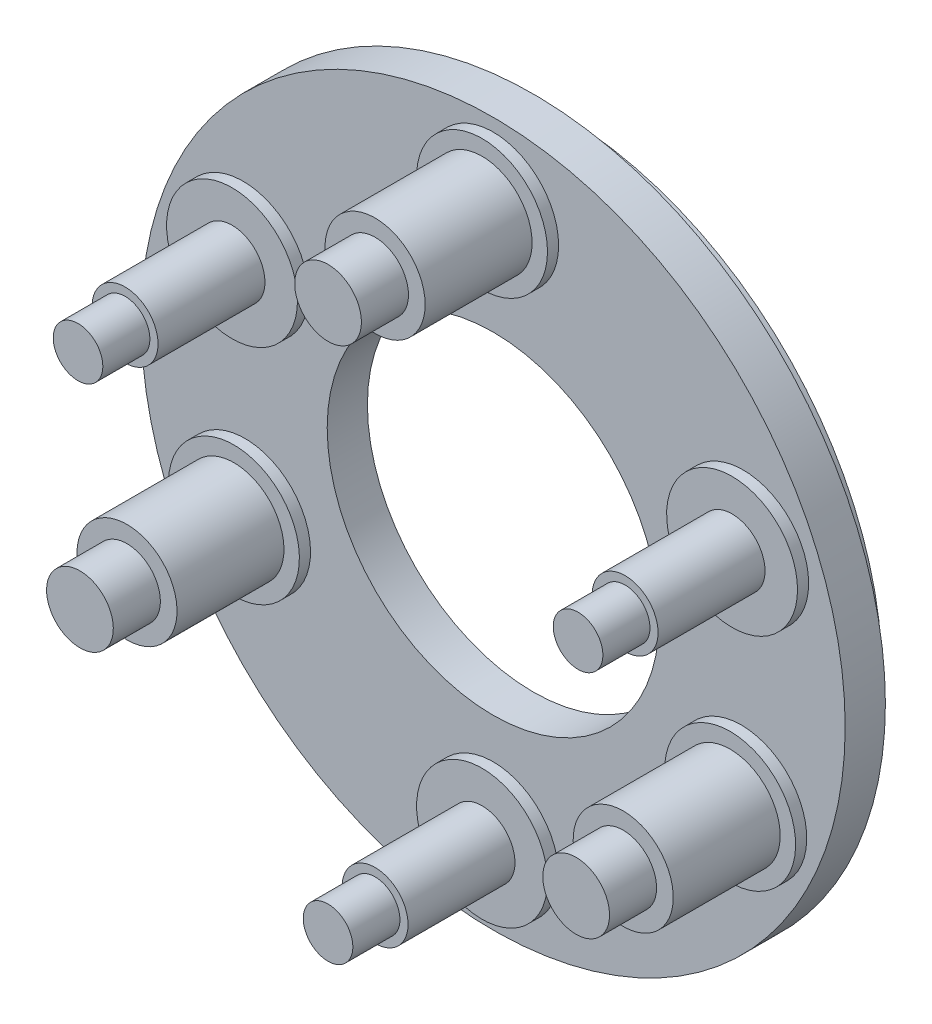
SolidWorks part; units mm, degrees
material "PE Low/Medium Density"
ref_plane "Front Plane" through (0, 0, 0) normal (0, 0, 1) x (1, 0, 0)
ref_plane "Top Plane" through (0, 0, 0) normal (0, 1, 0) x (1, 0, 0)
ref_plane "Right Plane" through (0, 0, 0) normal (1, 0, 0) x (0, 0, -1)
sketch "Sketch1" plane through (0, 0, 0) normal (0, 0, 1) x (1, 0, 0)
  circle A0 centre (0, 0) radius 10.4521
  circle A1 centre (0, 0) radius 4.9276
  dimension "D1" = 20.9042
  dimension "D2" = 9.8552
extrude "Base" add sketch "Sketch1" along normal blind 1.1938
sketch "Sketch2" plane through (0, 0, 0) normal (0, 0, -1) x (-1, 0, 0)
  circle A0 centre (0, 0) radius 9.6393
  circle A1 centre (0, 0) radius 8.89
  dimension "D1" = 17.78
  dimension "D2" = 0.7493
extrude "Track" add sketch "Sketch2" along normal blind 0.7112
sketch "Sketch3" plane through (0, 0, 1.1938) normal (0, 0, 1) x (1, 0, 0)
  line L0 (0, 0) -> (0, 10.4521) construction
  line L1 (0, 10.4521) -> (0, 0) construction
  circle A0 centre (0, 0) radius 10.4521 construction
  circle A1 centre (0, 8.128) radius 1.9431
  dimension "D1" = 3.8862
  dimension "D2" = 8.128
extrude "Platform A1" add sketch "Sketch3" along normal blind 0.3302
sketch "Sketch4" plane through (0, 0, 1.524) normal (0, 0, 1) x (1, 0, 0)
  circle A0 centre (0, 8.128) radius 1.4859
  dimension "D1" = 2.9718
extrude "Platform A2" add sketch "Sketch4" along normal blind 3.175
sketch "Sketch5" plane through (0, 0, 4.699) normal (0, 0, 1) x (1, 0, 0)
  circle A0 centre (0, 8.128) radius 0.9906
  dimension "D1" = 1.9812
extrude "Platform A3" add sketch "Sketch5" along normal blind 1.397
pattern_circular "CCW pattern for platform A" count 2 every 115 about axis through (0, 0, 1.1938) along (0, 0, 1) of "Platform A1", "Platform A2", "Platform A3"
pattern_circular "CW pattern for platform A" count 2 every 115 about axis through (0, 0, 1.1938) along (0, 0, 1) of "Platform A1", "Platform A2", "Platform A3"
sketch "Sketch6" plane through (0, 0, 1.1938) normal (0, 0, 1) x (1, 0, 0)
  line L0 (0, 0) -> (0, -10.4521) construction
  circle A0 centre (0, 0) radius 10.4521 construction
  circle A1 centre (0, -8.0645) radius 1.9431
  dimension "D1" = 3.8862
  dimension "D2" = 8.0645
extrude "Platform B1" add sketch "Sketch6" along normal blind 0.3302
sketch "Sketch7" plane through (0, 0, 1.524) normal (0, 0, 1) x (1, 0, 0)
  line L0 (0, 0) -> (0, -10.4521) construction
  circle A0 centre (0, 0) radius 10.4521 construction
  circle A1 centre (0, -8.0645) radius 0.9779
  dimension "D1" = 1.9558
extrude "Platform B2" add sketch "Sketch7" along normal blind 3.175
sketch "Sketch8" plane through (0, 0, 4.699) normal (0, 0, 1) x (1, 0, 0)
  circle A0 centre (0, -8.0645) radius 0.7366
  dimension "D1" = 1.4732
extrude "Platform B3" add sketch "Sketch8" along normal blind 1.397
pattern_circular "CCW pattern for platform B" count 2 every 113 about axis through (0, 0, 1.1938) along (0, 0, 1) of "Platform B1", "Platform B2", "Platform B3"
pattern_circular "CW pattern for platform B" count 2 every 113 about axis through (0, 0, 1.1938) along (0, 0, 1) of "Platform B1", "Platform B2", "Platform B3"
